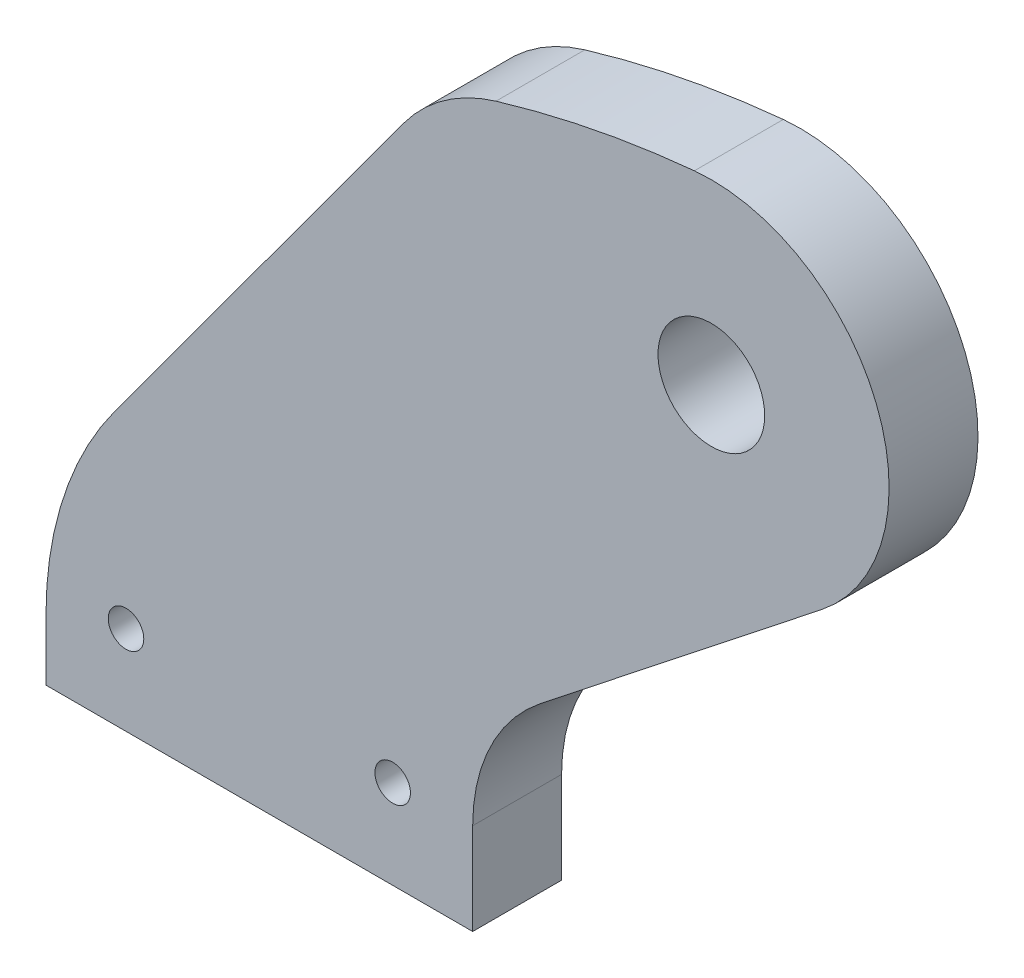
SolidWorks part; units mm, degrees
ref_plane "Front Plane" through (0, 0, 0) normal (0, 0, 1) x (1, 0, 0)
ref_plane "Top Plane" through (0, 0, 0) normal (0, 1, 0) x (1, 0, 0)
ref_plane "Right Plane" through (0, 0, 0) normal (1, 0, 0) x (0, 0, -1)
sketch "Sketch1" plane through (0, 0, 0) normal (0, 0, 1) x (1, 0, 0)
  line L0 (-7.62, 0) -> (7.62, 0)
  line L1 (-7.62, 0) -> (-7.62, 2.1924)
  line L2 (-5.1613, 9.7027) -> (5.1582, 23.7748)
  line L3 (6.35, 25.4) -> (31.75, 25.4) construction
  line L4 (20.0791, 16.1861) -> (10.0353, 8.2568)
  line L5 (7.62, 3.2728) -> (7.62, 0)
  line L6 (-7.62, 6.35) -> (7.62, 6.35) construction
  line L7 (0, 6.35) -> (19.05, 25.4) construction
  line L8 (-7.62, 3.175) -> (7.6208, 3.175) construction
  line L9 (0, 6.35) -> (0, 0) construction
  arc A0 (-7.62, 2.1924) -> (-5.1613, 9.7027) centre (5.08, 2.1924) cw
  arc A1 (10.0353, 8.2568) -> (7.62, 3.2728) centre (13.97, 3.2728) ccw
  circle A2 centre (19.05, 25.4) radius 2.54 construction
  arc A3 (8.4515, 26.101) -> (15.539, 27.4912) centre (19.05, -9.1711) cw
  arc A4 (5.1582, 23.7748) -> (8.4515, 26.101) centre (10.2789, 20.0196) cw
  arc A5 (15.539, 27.4912) -> (20.0791, 16.1861) centre (16.1443, 21.1701) cw
  circle A6 centre (-4.7625, 3.175) radius 0.635
  circle A7 centre (4.7625, 3.175) radius 0.635
  dimension "D6" = 12.7
  dimension "D7" = 6.35
  dimension "D8" = 5.08
  dimension "D9" = 36.83
  dimension "D10" = 6.35
  dimension "D12" = 1.27
  dimension "D13" = 9.525
  dimension "D1" = 25.4
  dimension "D2" = 15.24
  dimension "D3" = 25.4
  dimension "D4" = 19.05
  dimension "D5" = 6.35
  dimension "D11" = 3.175
extrude "Extrude1" add sketch "Sketch1" along normal blind 3.175
sketch "Sketch2" plane through (0, 0, 3.175) normal (0, 0, 1) x (1, 0, 0)
  circle A0 centre (16.1443, 21.1701) radius 1.905
  dimension "D1" = 3.81
extrude "Extrude2" cut sketch "Sketch2" against normal through all
